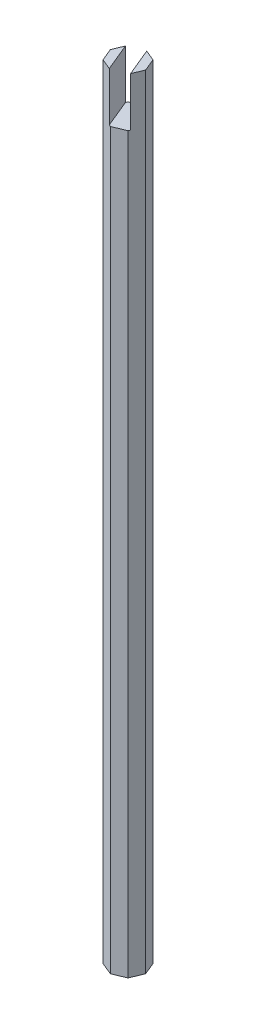
SolidWorks part; units mm, degrees
ref_plane "Front Plane" through (0, 0, 0) normal (0, 0, 1) x (1, 0, 0)
ref_plane "Top Plane" through (0, 0, 0) normal (0, 1, 0) x (1, 0, 0)
ref_plane "Right Plane" through (0, 0, 0) normal (1, 0, 0) x (0, 0, -1)
sketch "Sketch1" plane through (0, 0, 0) normal (0, 1, 0) x (1, 0, 0)
  line L1 (13.7464, 0) -> (9.7202, 9.7202)
  line L2 (9.7202, 9.7202) -> (0, 13.7464)
  line L3 (0, 13.7464) -> (-9.7202, 9.7202)
  line L4 (-9.7202, 9.7202) -> (-13.7464, 0)
  line L5 (-13.7464, 0) -> (-9.7202, -9.7202)
  line L6 (-9.7202, -9.7202) -> (0, -13.7464)
  line L7 (0, -13.7464) -> (9.7202, -9.7202)
  line L8 (9.7202, -9.7202) -> (13.7464, 0)
  circle A0 centre (0, 0) radius 12.7 construction
  dimension "D1" = 25.4
extrude "Boss-Extrude1" add sketch "Sketch1" along normal blind 609.6
sketch "Sketch2" plane through (0, 609.6, 0) normal (0, 1, 0) x (1, 0, 0)
  line L0 (-1.0066, -14.1633) -> (-10.7267, 9.3032)
  line L1 (-1.0066, -14.1633) -> (10.7267, -9.3032)
  line L2 (-10.7267, 9.3032) -> (1.0066, 14.1633)
  line L3 (10.7267, -9.3032) -> (1.0066, 14.1633)
  line L4 (-1.0066, -14.1633) -> (1.0066, 14.1633) construction
  line L5 (-10.7267, 9.3032) -> (10.7267, -9.3032) construction
  line L6 (0, 13.7464) -> (-9.7202, 9.7202) construction
  point P1 (0, 0)
  dimension "D1" = 12.7
  dimension "D2" = 180
extrude "Cut-Extrude1" cut sketch "Sketch2" against normal blind 38.1
